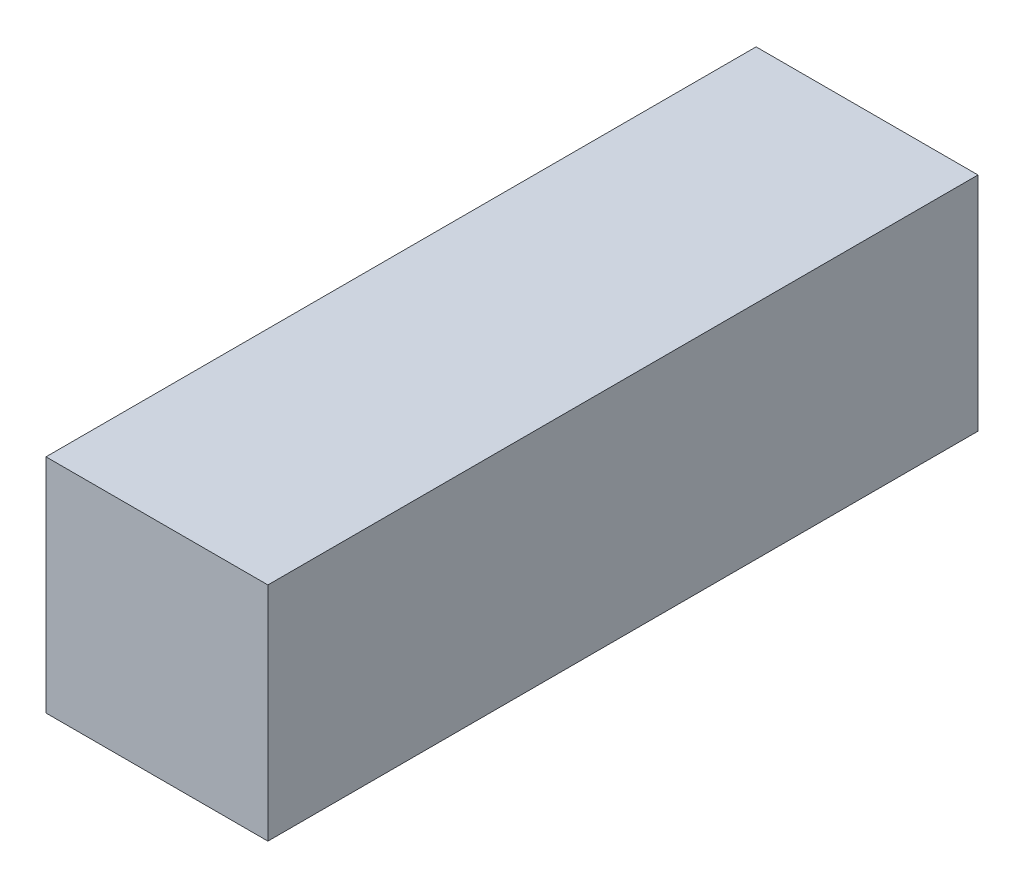
SolidWorks part; units mm, degrees
ref_plane "Front Plane" through (0, 0, 0) normal (0, 0, 1) x (1, 0, 0)
ref_plane "Top Plane" through (0, 0, 0) normal (0, 1, 0) x (1, 0, 0)
ref_plane "Right Plane" through (0, 0, 0) normal (1, 0, 0) x (0, 0, -1)
sketch "Sketch1" plane through (0, 0, 0) normal (0, 0, 1) x (1, 0, 0)
  line L1 (-17.5, -17.5) -> (17.5, -17.5)
  line L2 (-17.5, -17.5) -> (-17.5, 17.5)
  line L3 (-17.5, 17.5) -> (17.5, 17.5)
  line L4 (17.5, -17.5) -> (17.5, 17.5)
  line L5 (-17.5, -17.5) -> (17.5, 17.5) construction
  line L6 (-17.5, 17.5) -> (17.5, -17.5) construction
  point P0 (0, 0)
  dimension "D1" = 35
  dimension "D2" = 35
extrude "Boss-Extrude1" add sketch "Sketch1" along normal blind 112
sketch "Sketch2" plane through (0, 0, 112) normal (0, 0, 1) x (1, 0, 0)
  circle A0 centre (0, 0) radius 24.7487
